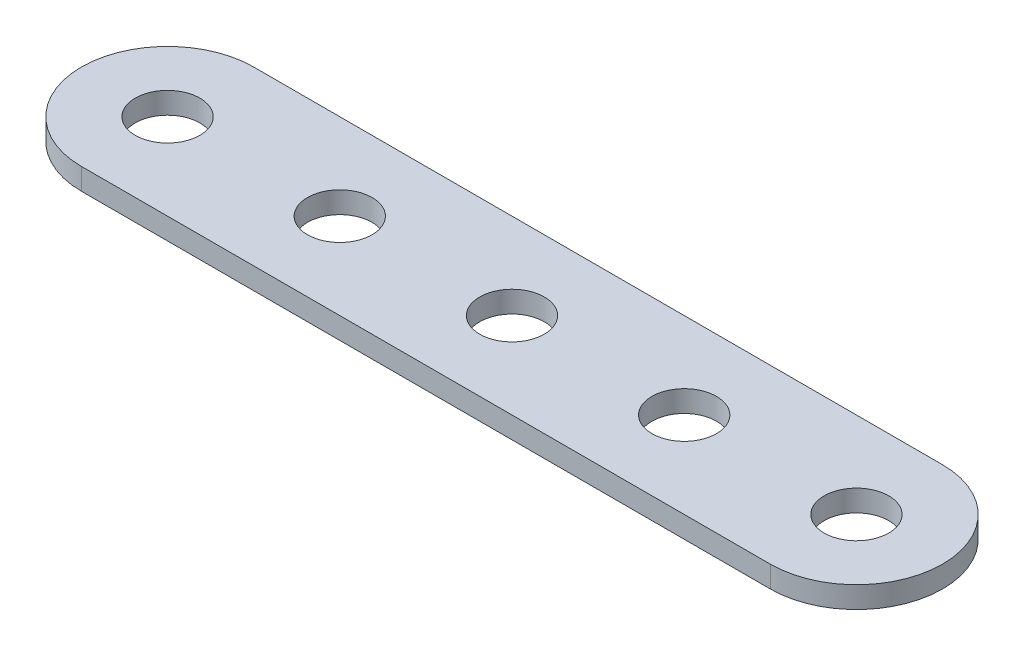
SolidWorks part; units mm, degrees
ref_plane "Front Plane" through (0, 0, 0) normal (0, 0, 1) x (1, 0, 0)
ref_plane "Top Plane" through (0, 0, 0) normal (0, 1, 0) x (1, 0, 0)
ref_plane "Right Plane" through (0, 0, 0) normal (1, 0, 0) x (0, 0, -1)
sketch "Sketch1" plane through (0, 0, 0) normal (0, 1, 0) x (1, 0, 0)
  line L1 (-25.4, -6.35) -> (25.4, -6.35)
  line L3 (-25.4, 6.35) -> (25.4, 6.35)
  line L5 (-28.2847, -5.6569) -> (28.2847, 5.6569) construction
  line L6 (-28.2847, 5.6569) -> (28.2847, -5.6569) construction
  arc A0 (-25.4, 6.35) -> (-25.4, -6.35) centre (-25.4, 0) ccw
  arc A1 (25.4, -6.35) -> (25.4, 6.35) centre (25.4, 0) ccw
  circle A2 centre (-25.4, 0) radius 2.3813
  circle A3 centre (-12.7, 0) radius 2.3813
  circle A4 centre (0, 0) radius 2.3813
  circle A5 centre (12.7, 0) radius 2.3813
  circle A6 centre (25.4, 0) radius 2.3813
  point P0 (0, 0)
  dimension "D3" = 12.7
  dimension "D1" = 4.7625
  dimension "D2" = 4.7625
  dimension "D4" = 4.7625
  dimension "D5" = 4.7625
  dimension "D6" = 4.7625
  dimension "D7" = 12.7
  dimension "D8" = 12.7
  dimension "D9" = 12.7
  dimension "D10" = 12.7
extrude "Boss-Extrude1" add sketch "Sketch1" along normal blind 1.5875
